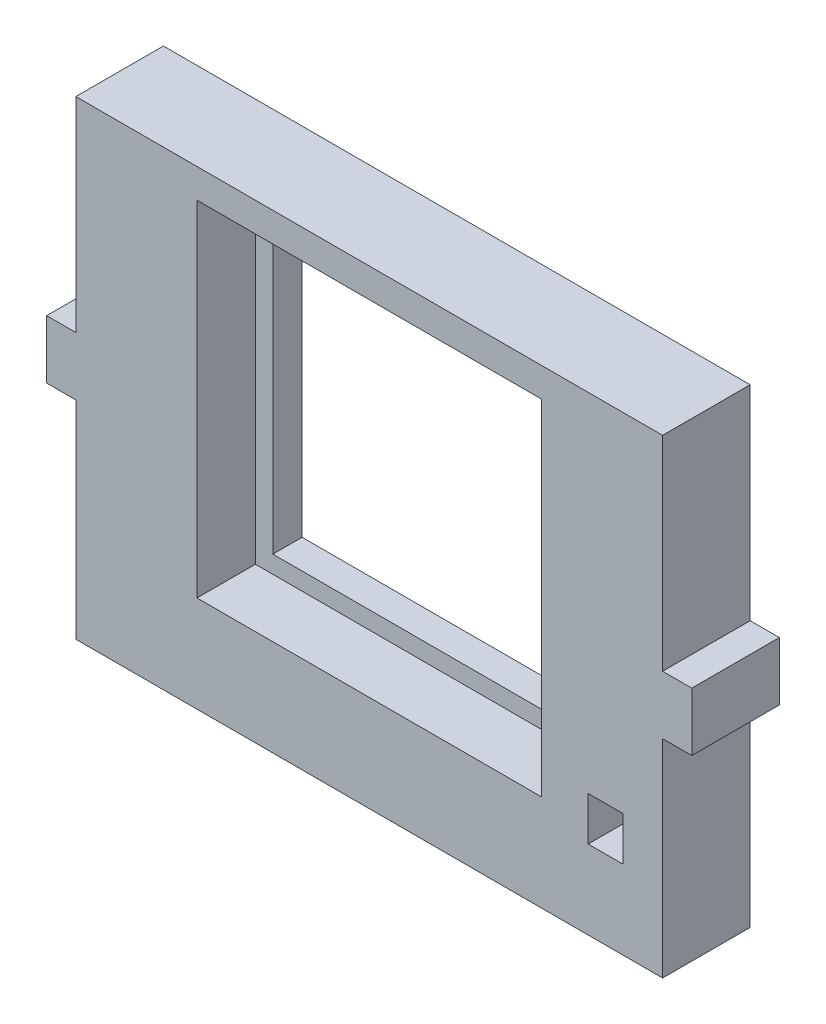
SolidWorks part; units mm, degrees
ref_plane "前基準面" through (0, 0, 0) normal (0, 0, 1) x (1, 0, 0)
ref_plane "上基準面" through (0, 0, 0) normal (0, 1, 0) x (1, 0, 0)
ref_plane "右基準面" through (0, 0, 0) normal (1, 0, 0) x (0, 0, -1)
sketch "草圖1" plane through (0, 0, 0) normal (0, 0, 1) x (1, 0, 0)
  line L1 (-59.8055, 34.946) -> (40.6945, 34.946)
  line L2 (-59.8055, 34.946) -> (-59.8055, -45.554)
  line L3 (-59.8055, -45.554) -> (40.6945, -45.554)
  line L4 (40.6945, 34.946) -> (40.6945, -45.554)
  line L5 (-59.8055, -0.054) -> (-64.8055, -0.054)
  line L6 (-59.8055, -0.054) -> (-59.8055, -10.054)
  line L7 (-59.8055, -10.054) -> (-64.8055, -10.054)
  line L8 (-64.8055, -0.054) -> (-64.8055, -10.054)
  line L9 (40.6945, -0.054) -> (45.6945, -0.054)
  line L10 (40.6945, -0.054) -> (40.6945, -10.054)
  line L11 (40.6945, -10.054) -> (45.6945, -10.054)
  line L12 (45.6945, -0.054) -> (45.6945, -10.054)
  line L13 (-36.0555, 26.946) -> (16.9445, 26.946)
  line L14 (-36.0555, 26.946) -> (-36.0555, -26.054)
  line L15 (-36.0555, -26.054) -> (16.9445, -26.054)
  line L16 (16.9445, 26.946) -> (16.9445, -26.054)
  line L17 (27.9445, -32.054) -> (33.9445, -32.054)
  line L18 (27.9445, -32.054) -> (27.9445, -24.554)
  line L19 (27.9445, -24.554) -> (33.9445, -24.554)
  line L20 (33.9445, -32.054) -> (33.9445, -24.554)
  point P20 (27.9445, -28.304)
  dimension "D1" = 100.5
  dimension "D2" = 35
  dimension "80.5" = 80.5
  dimension "D3" = 35
  dimension "D4" = 5
  dimension "D5" = 10
  dimension "D6" = 10
  dimension "D7" = 5
  dimension "D8" = 8
  dimension "D9" = 53
  dimension "D10" = 53
  dimension "D11" = 23.75
  dimension "D12" = 7.5
  dimension "D13" = 6
  dimension "D14" = 11
extrude "填料-伸長1" add sketch "草圖1" along normal blind 15 contours L5 L8 L7 L2 | L4 L1 L2 L3 L20 L17 L18 L19 L13 L16 L15 L14 | L12 L9 L4 L11
sketch "草圖2" plane through (0, 0, 15) normal (0, 0, 1) x (1, 0, 0)
  line L0 (-59.8055, 34.946) -> (40.6945, 34.946) construction
  line L1 (-39.0555, 29.946) -> (19.9445, 29.946)
  line L2 (-39.0555, 29.946) -> (-39.0555, -29.054)
  line L3 (-39.0555, -29.054) -> (19.9445, -29.054)
  line L4 (19.9445, 29.946) -> (19.9445, -29.054)
  line L5 (-59.8055, 34.946) -> (-59.8055, -0.054) construction
  dimension "D1" = 5
  dimension "D2" = 20.75
  dimension "D3" = 59
  dimension "D4" = 59
extrude "除料-伸長1" cut sketch "草圖2" against normal blind 10
